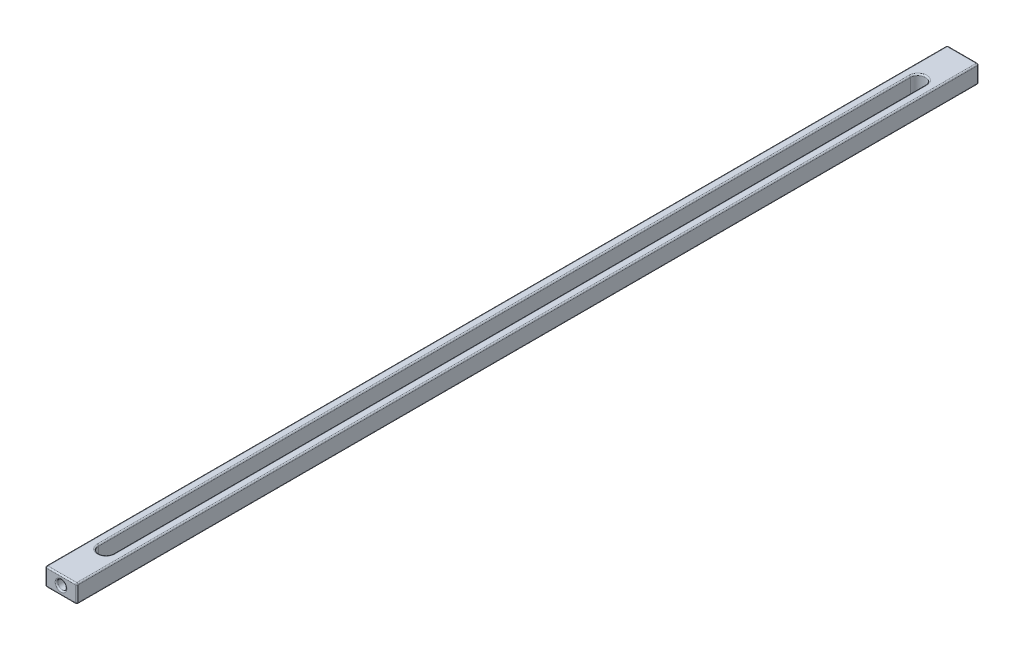
SolidWorks part; units mm, degrees
ref_plane "Plan de face" through (0, 0, 0) normal (0, 0, 1) x (1, 0, 0)
ref_plane "Plan de dessus" through (0, 0, 0) normal (0, 1, 0) x (1, 0, 0)
ref_plane "Plan de droite" through (0, 0, 0) normal (1, 0, 0) x (0, 0, -1)
sketch "Esquisse1" plane through (0, 0, 0) normal (0, 0, 1) x (1, 0, 0)
  line L0 (3.85, 0) -> (-3.85, 0) construction
  line L1 (-3.5, -2) -> (3.5, -2)
  line L2 (-3.5, -2) -> (-3.5, 2)
  line L3 (-3.5, 2) -> (3.5, 2)
  line L4 (3.5, -2) -> (3.5, 2)
  line L5 (-3.5, -2) -> (3.5, 2) construction
  line L6 (-3.5, 2) -> (3.5, -2) construction
  point P1 (0, 0)
  dimension "D1" = 4
  dimension "D2" = 7
extrude "Boss.-Extru.1" add sketch "Esquisse1" along normal blind 200
sketch "Esquisse2" plane through (0, 2, 0) normal (0, 1, 0) x (1, 0, 0)
  line L0 (0, -190) -> (0, -10) construction
  line L1 (0, -1.1) -> (0, 1.1) construction
  line L2 (-1.65, -190) -> (-1.65, -10)
  line L3 (1.65, -190) -> (1.65, -10)
  line L4 (3.5, -200) -> (-3.5, -200) construction
  line L5 (-1.1, 0) -> (1.1, 0) construction
  arc A0 (-1.65, -190) -> (1.65, -190) centre (0, -190) ccw
  arc A1 (1.65, -10) -> (-1.65, -10) centre (0, -10) ccw
  point P5 (0, -100)
  dimension "D1" = 10
  dimension "D3" = 1.65
  dimension "D2" = 10
extrude "Enlèv. mat.-Extru.1" cut sketch "Esquisse2" against normal through all
sketch "Esquisse5" plane through (0, 0, 200) normal (0, 0, 1) x (1, 0, 0)
  circle A0 centre (0, 0) radius 1
  dimension "D1" = 2
extrude "Enlèv. mat.-Extru.3" cut sketch "Esquisse5" along normal through all and the other way up to next
sketch3d "Esquisse3D2"
  line L0 (1.65, -2, 190) -> (1.65, 2, 190) construction
fillet "Congé6" radius 0.3
